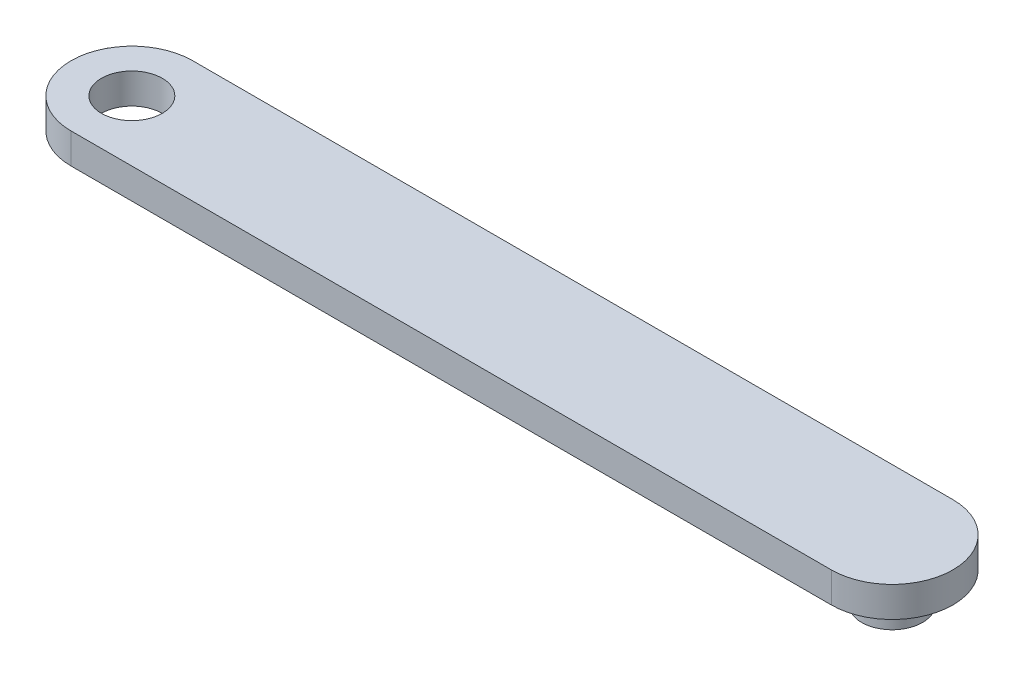
SolidWorks part; units mm, degrees
ref_plane "Front Plane" through (0, 0, 0) normal (0, 0, 1) x (1, 0, 0)
ref_plane "Top Plane" through (0, 0, 0) normal (0, 1, 0) x (1, 0, 0)
ref_plane "Right Plane" through (0, 0, 0) normal (1, 0, 0) x (0, 0, -1)
sketch "Sketch1" plane through (0, 0, 0) normal (0, 1, 0) x (1, 0, 0)
  line L0 (-12.5, 0) -> (12.5, 0) construction
  line L1 (-12.5, 2) -> (12.5, 2)
  line L2 (-12.5, -2) -> (12.5, -2)
  arc A0 (-12.5, 2) -> (-12.5, -2) centre (-12.5, 0) ccw
  arc A1 (12.5, -2) -> (12.5, 2) centre (12.5, 0) ccw
  circle A2 centre (-12.5, 0) radius 1
  circle A3 centre (12.5, 0) radius 1
  point P3 (0, 0)
  dimension "D3" = 2
  dimension "D4" = 2
  dimension "D1" = 25
  dimension "D2" = 4
extrude "Boss-Extrude2" add sketch "Sketch1" along normal blind 1
sketch "Sketch2" plane through (0, 0, 0) normal (0, 1, 0) x (1, 0, 0)
  circle A0 centre (16.5, 0) radius 1
  dimension "D1" = 2
  dimension "D2" = 16.5
sketch "Sketch3" plane through (0, 0, 0) normal (0, -1, 0) x (-1, 0, 0)
  circle A0 centre (-16.5, 0) radius 0.9999
sketch "Sketch5" plane through (0, 0, 0) normal (0, -1, 0) x (1, 0, 0)
  circle A0 centre (12.5, 0) radius 1
  dimension "D1" = 2
  dimension "D2" = 12.5
extrude "Boss-Extrude3" add sketch "Sketch5" along normal blind 1
